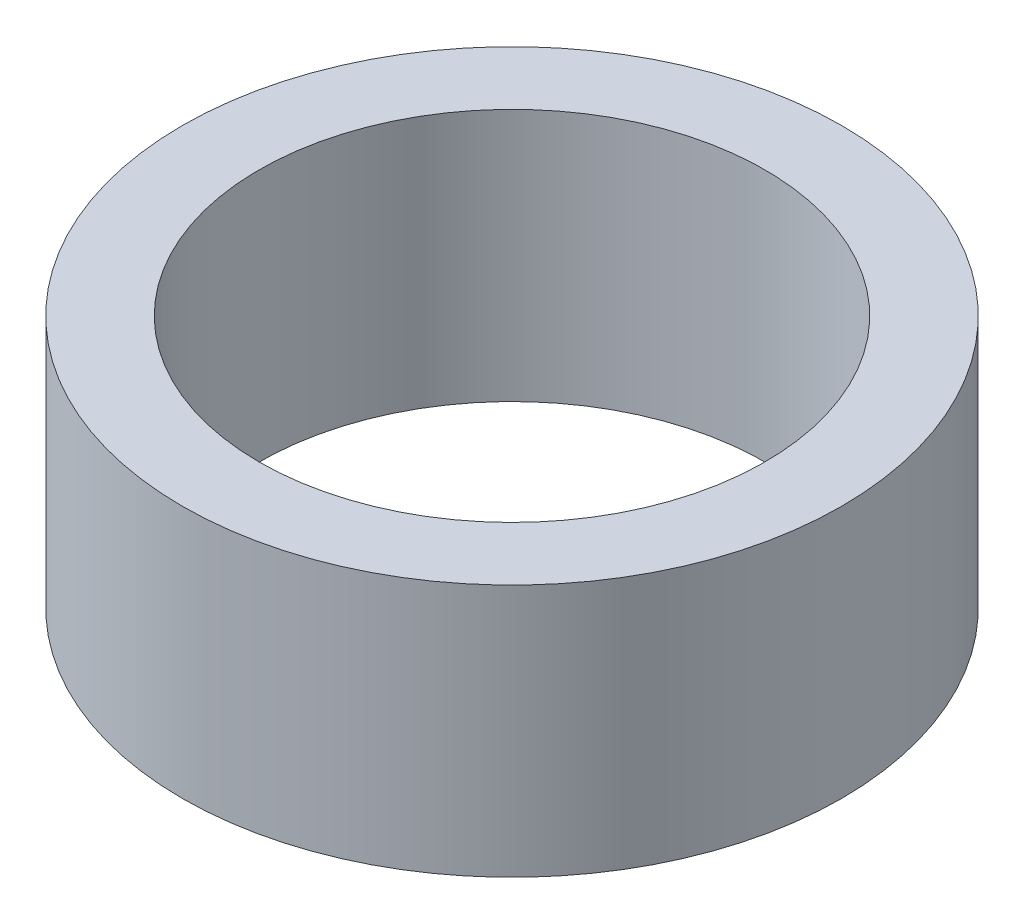
SolidWorks part; units mm, degrees
ref_plane "Front Plane" through (0, 0, 0) normal (0, 0, 1) x (1, 0, 0)
ref_plane "Top Plane" through (0, 0, 0) normal (0, 1, 0) x (1, 0, 0)
ref_plane "Right Plane" through (0, 0, 0) normal (1, 0, 0) x (0, 0, -1)
sketch "Sketch1" plane through (0, 0, 0) normal (0, 1, 0) x (1, 0, 0)
  circle A0 centre (0, 0) radius 18.415
  circle A1 centre (0, 0) radius 24
  dimension "D1" = 36.83
  dimension "D2" = 48
extrude "Boss-Extrude1" add sketch "Sketch1" along normal blind 18.422
